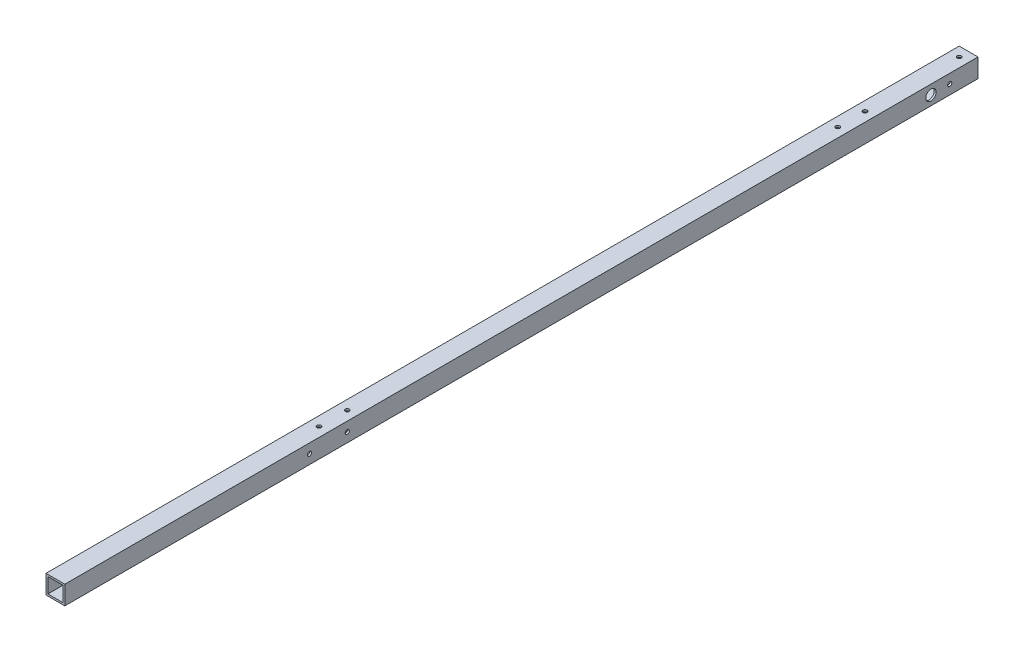
SolidWorks part; units mm, degrees
ref_plane "正面" through (0, 0, 0) normal (0, 0, 1) x (1, 0, 0)
ref_plane "平面" through (0, 0, 0) normal (0, 1, 0) x (1, 0, 0)
ref_plane "右側面" through (0, 0, 0) normal (1, 0, 0) x (0, 0, -1)
sketch "ｽｹｯﾁ1" plane through (0, 0, 0) normal (0, 0, 1) x (1, 0, 0)
  line L1 (-10, 10) -> (10, 10)
  line L2 (-10, 10) -> (-10, -10)
  line L3 (-10, -10) -> (10, -10)
  line L4 (10, 10) -> (10, -10)
  line L5 (-10, 10) -> (10, -10) construction
  line L6 (-10, -10) -> (10, 10) construction
  line L7 (-8, 8) -> (8, 8)
  line L8 (-8, 8) -> (-8, -8)
  line L9 (-8, -8) -> (8, -8)
  line L10 (8, 8) -> (8, -8)
  line L11 (-8, 8) -> (8, -8) construction
  line L12 (-8, -8) -> (8, 8) construction
  point P0 (0, 0)
  point P6 (0, 0)
  dimension "D1" = 20
  dimension "D2" = 20
  dimension "D3" = 16
  dimension "D4" = 16
extrude "ﾎﾞｽ - 押し出し1" add sketch "ｽｹｯﾁ1" along normal blind 970
sketch "ｽｹｯﾁ2" plane through (10, 0, 0) normal (1, 0, 0) x (0, 0, -1)
  line L0 (-970, 0) -> (-710, 0)
  line L1 (-970, -10) -> (-970, 10) construction
  line L2 (-710, 0) -> (-890.4665, 0)
  line L3 (-890.4665, 0) -> (-845.8821, 0)
  line L4 (-845.8821, 0) -> (-803.5394, 0)
  line L5 (-710, 0) -> (-670, 0)
  line L6 (-670, 0) -> (-50, 0)
  line L7 (-50, 0) -> (-30, 0)
  circle A0 centre (-710, 0) radius 2.2
  circle A4 centre (-670, 0) radius 2.2
  circle A5 centre (-50, 0) radius 5.5
  circle A6 centre (-30, 0) radius 2.2
  dimension "D5" = 4.4
  dimension "D6" = 11
  dimension "D7" = 4.4
  dimension "D8" = 4.4
  dimension "D1" = 260
  dimension "D2" = 40
  dimension "D3" = 620
  dimension "D4" = 20
extrude "ｶｯﾄ - 押し出し1" cut sketch "ｽｹｯﾁ2" against normal blind 970
sketch "ｽｹｯﾁ3" plane through (0, 10, 0) normal (0, 1, 0) x (1, 0, 0)
  line L0 (0, -970) -> (0, -690)
  line L1 (10, -970) -> (-10, -970) construction
  line L2 (0, -690) -> (0, -660)
  line L3 (0, -660) -> (0, -10)
  circle A0 centre (0, -690) radius 2.2
  circle A1 centre (0, -660) radius 2.2
  circle A2 centre (0, -10) radius 2.2
  dimension "D2" = 4.4
  dimension "D4" = 4.4
  dimension "D6" = 4.4
  dimension "D1" = 280
  dimension "D3" = 30
  dimension "D5" = 650
extrude "ｶｯﾄ - 押し出し2" cut sketch "ｽｹｯﾁ3" against normal blind 970
sketch "ｽｹｯﾁ4" plane through (0, 10, 0) normal (0, 1, 0) x (1, 0, 0)
  line L0 (0, 0) -> (0, -110)
  line L2 (0, -110) -> (0, -95.5)
  line L3 (0, -110) -> (0, -124.5)
  circle A0 centre (0, -95.5) radius 2.2
  circle A1 centre (0, -124.5) radius 2.2
  dimension "D5" = 4.4
  dimension "D6" = 4.4
  dimension "D1" = 110
  dimension "D2" = 14.5
  dimension "D3" = 0
  dimension "D4" = 14.5
sketch "ｽｹｯﾁ5" plane through (0, 10, 0) normal (0, 1, 0) x (1, 0, 0)
  line L0 (0, -110) -> (0, -139)
  circle A0 centre (0, -110) radius 2.2
  circle A1 centre (0, -139) radius 2.2
  dimension "D1" = 4.4
  dimension "D3" = 4.4
  dimension "D2" = 29
extrude "ｶｯﾄ - 押し出し4" cut sketch "ｽｹｯﾁ5" against normal blind 30
